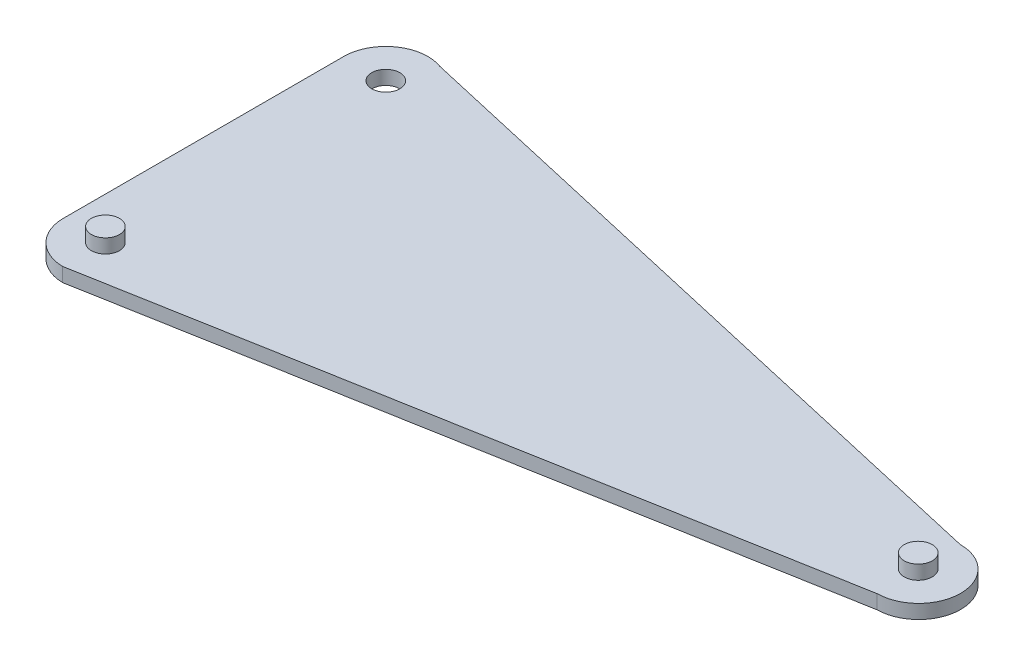
SolidWorks part; units mm, degrees
ref_plane "Front Plane" through (0, 0, 0) normal (0, 0, 1) x (1, 0, 0)
ref_plane "Top Plane" through (0, 0, 0) normal (0, 1, 0) x (1, 0, 0)
ref_plane "Right Plane" through (0, 0, 0) normal (1, 0, 0) x (0, 0, -1)
sketch "Sketch1" plane through (0, 0, 0) normal (0, 1, 0) x (1, 0, 0)
  line L0 (-47.6829, 11.1642) -> (-47.6829, -8.8358)
  line L1 (-43.6576, 13.9836) -> (4.4626, 3)
  line L2 (-44.7526, -11.835) -> (4.5128, -2.9996)
  circle A0 centre (-44.6829, 11.1642) radius 1
  circle A1 centre (-44.6829, -8.8358) radius 1
  circle A2 centre (4.4626, 0) radius 1
  arc A3 (-43.6576, 13.9836) -> (-47.6829, 11.1642) centre (-44.6829, 11.1642) ccw
  arc A4 (-44.7526, -11.835) -> (-47.6829, -8.8358) centre (-44.6829, -8.8358) cw
  arc A5 (4.4626, 3) -> (4.5128, -2.9996) centre (4.4877, 0.0002) cw
  dimension "D5" = 2
  dimension "D6" = 2
  dimension "D1" = 2
  dimension "D2" = 3
  dimension "D3" = 3
  dimension "D4" = 3
  dimension "D7" = 20
  dimension "D8" = 3
  dimension "D9" = 3
extrude "Boss-Extrude5" add sketch "Sketch1" along normal blind 1
sketch "Sketch2" plane through (0, 1, 0) normal (0, 1, 0) x (1, 0, 0)
  circle A0 centre (-44.6829, 11.1642) radius 1
  circle A1 centre (-44.6829, -8.8358) radius 1
sketch "Sketch3" plane through (0, 1, 0) normal (0, 1, 0) x (1, 0, 0)
  circle A0 centre (4.4626, 0) radius 1
  dimension "D1" = 2
extrude "Boss-Extrude6" add sketch "Sketch3" along normal mid plane 1
sketch "Sketch4" plane through (0, 1, 0) normal (0, 1, 0) x (1, 0, 0)
  circle A0 centre (4.4626, 0) radius 1.0641
sketch "Sketch5" plane through (0, 1, 0) normal (0, 1, 0) x (1, 0, 0)
  circle A0 centre (4.4626, 0) radius 1
extrude "Boss-Extrude8" add sketch "Sketch5" along normal blind 1
sketch "Sketch6" plane through (0, 1, 0) normal (0, 1, 0) x (1, 0, 0)
  circle A0 centre (-44.6829, -8.8358) radius 1
extrude "Boss-Extrude9" add sketch "Sketch6" along normal mid plane 2
